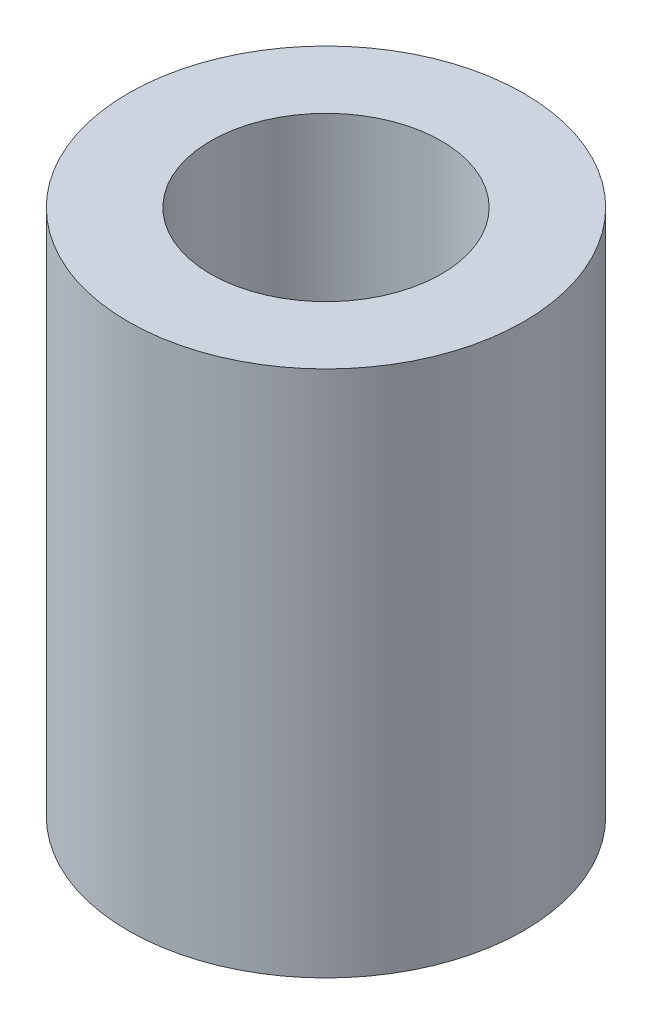
SolidWorks part; units mm, degrees
ref_plane "Front Plane" through (0, 0, 0) normal (0, 0, 1) x (1, 0, 0)
ref_plane "Top Plane" through (0, 0, 0) normal (0, 1, 0) x (1, 0, 0)
ref_plane "Right Plane" through (0, 0, 0) normal (1, 0, 0) x (0, 0, -1)
sketch "Sketch1" plane through (0, 0, 0) normal (0, 1, 0) x (1, 0, 0)
  circle A0 centre (0, 0) radius 1.75
  circle A1 centre (0, 0) radius 3
  dimension "D1" = 3.5
  dimension "D2" = 6
extrude "Boss-Extrude1" add sketch "Sketch1" along normal mid plane 8
